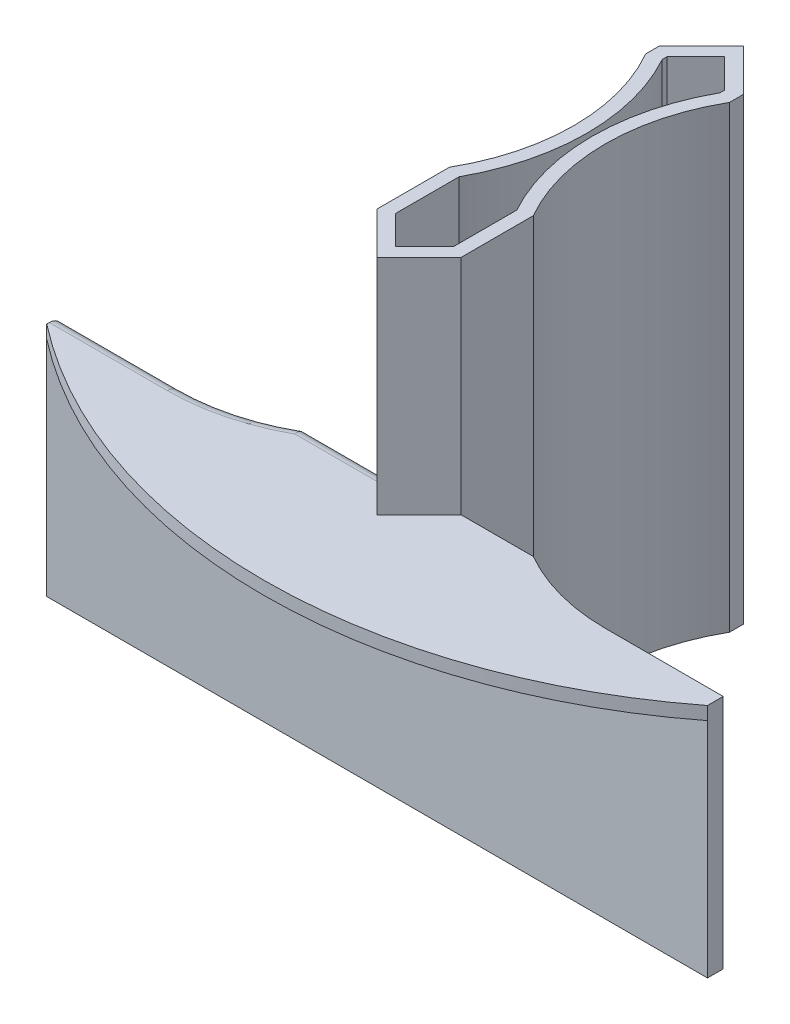
SolidWorks part; units mm, degrees
ref_plane "Front Plane" through (0, 0, 0) normal (0, 0, 1) x (1, 0, 0)
ref_plane "Top Plane" through (0, 0, 0) normal (0, 1, 0) x (1, 0, 0)
ref_plane "Right Plane" through (0, 0, 0) normal (1, 0, 0) x (0, 0, -1)
sketch "Sketch1" plane through (0, 0, 0) normal (0, 1, 0) x (1, 0, 0)
  line L0 (23.7595, 41.275) -> (41.275, 41.275) construction
  line L1 (-41.275, -41.275) -> (-23.7595, -41.275) construction
  line L2 (-41.275, -41.275) -> (-41.275, -23.7595) construction
  line L3 (-41.275, 41.275) -> (-23.7595, 41.275) construction
  line L4 (41.275, -41.275) -> (41.275, -23.7595) construction
  line L5 (-41.275, -41.275) -> (41.275, 41.275) construction
  line L6 (-41.275, 41.275) -> (41.275, -41.275) construction
  line L7 (41.275, 23.7595) -> (41.275, 41.275) construction
  line L8 (-41.275, 23.7595) -> (-41.275, 41.275) construction
  line L9 (23.7595, -41.275) -> (41.275, -41.275) construction
  line L10 (24.7569, 45.085) -> (45.085, 45.085) construction
  line L11 (45.085, 24.7569) -> (45.085, 45.085) construction
  line L12 (45.085, -45.085) -> (45.085, -24.7569) construction
  line L13 (24.7569, -45.085) -> (45.085, -45.085) construction
  line L14 (-45.085, -45.085) -> (-24.7569, -45.085) construction
  line L15 (-45.085, -45.085) -> (-45.085, -24.7569) construction
  line L16 (-45.085, 24.7569) -> (-45.085, 45.085) construction
  line L17 (-45.085, 45.085) -> (-24.7569, 45.085) construction
  line L19 (-51.435, -51.435) -> (51.435, -51.435) construction
  line L20 (-51.435, -51.435) -> (-51.435, 51.435) construction
  line L21 (-51.435, 51.435) -> (51.435, 51.435) construction
  line L22 (51.435, -51.435) -> (51.435, 51.435) construction
  line L23 (-51.435, -51.435) -> (51.435, 51.435) construction
  line L24 (-51.435, 51.435) -> (51.435, -51.435) construction
  arc A1 (-41.275, 23.7595) -> (-41.275, -23.7595) centre (0, 0) ccw construction
  arc A2 (23.7595, 41.275) -> (-23.7595, 41.275) centre (0, 0) ccw construction
  arc A3 (-23.7595, -41.275) -> (23.7595, -41.275) centre (0, 0) ccw construction
  arc A4 (41.275, -23.7595) -> (41.275, 23.7595) centre (0, 0) ccw construction
  arc A5 (45.085, -24.7569) -> (45.085, 24.7569) centre (0, 0) ccw construction
  arc A6 (-24.7569, -45.085) -> (24.7569, -45.085) centre (0, 0) ccw construction
  arc A7 (-45.085, 24.7569) -> (-45.085, -24.7569) centre (0, 0) ccw construction
  arc A8 (24.7569, 45.085) -> (-24.7569, 45.085) centre (0, 0) ccw construction
  point P0 (0, 0)
  dimension "D1" = 82.55
  dimension "D2" = 82.55
  dimension "D3" = 95.25
  dimension "D4" = 3.81
sketch "Sketch2" plane through (0, 0, 0) normal (0, 0, 1) x (1, 0, 0)
  line L0 (0, 48) -> (0, 0) construction
  line L1 (0, 0) -> (0, -9.15) construction
  line L2 (0, 48) -> (0, 101.975) construction
  dimension "Cage height" = 48
  dimension "Plate height" = 53.975
  dimension "D1" = 57.15
  dimension "D2" = 9.15
sketch "Sketch13" plane through (0, 0, 0) normal (0, 1, 0) x (1, 0, 0)
  line L0 (-51.435, -51.435) -> (51.435, -51.435) construction
  line L1 (-41.275, -41.275) -> (-23.7595, -41.275) construction
  line L2 (-41.275, -41.275) -> (-41.275, -23.7595) construction
  line L4 (-51.435, -51.435) -> (0, -51.435)
  line L5 (-41.275, -41.275) -> (-23.7595, -41.275)
  line L6 (-41.275, -41.275) -> (-41.275, -23.7595)
  line L9 (0, -47.625) -> (0, -51.435)
  line L10 (-51.435, 51.435) -> (51.435, -51.435) construction
  line L11 (-41.275, 23.7595) -> (-41.275, 41.275) construction
  line L12 (-51.435, -51.435) -> (-51.435, 51.435) construction
  line L13 (-51.435, 51.435) -> (-41.275, 41.275)
  line L14 (-41.275, 23.7595) -> (-41.275, 41.275)
  line L15 (-51.435, -51.435) -> (-51.435, 51.435)
  arc A0 (-23.7595, -41.275) -> (23.7595, -41.275) centre (0, 0) ccw construction
  arc A2 (-23.7595, -41.275) -> (0, -47.625) centre (0, 0) ccw
  arc A4 (-41.275, 23.7595) -> (-41.275, -23.7595) centre (0, 0) ccw construction
  arc A5 (-41.275, 23.7595) -> (-41.275, -23.7595) centre (0, 0) ccw
extrude "Boss-Extrude2" add sketch "Sketch13" along normal up to vertex (101.975 mm away) and the other way up to vertex (9.15 mm away) up to point (0, 101.975, 0) other way up to point (0, -9.15, 0)
sketch "Sketch15" plane through (0, 101.975, 0) normal (0, 1, 0) x (1, 0, 0)
  line L0 (0, 0) -> (-51.435, -51.435)
  line L1 (-51.435, -51.435) -> (0, -51.435)
  line L2 (0, -51.435) -> (0, 0)
  line L3 (-51.435, -51.435) -> (51.435, -51.435) construction
extrude "Cut-Extrude2" cut sketch "Sketch15" against normal up to vertex (53.975 mm away) up to point (0, 48, 0)
mirror "Mirror1" about plane through (-51.435, 101.975, 51.435) normal (1, 0, 0) of "Boss-Extrude2", "Cut-Extrude2"
sketch "Sketch16" plane through (0, -9.15, 0) normal (0, -1, 0) x (1, 0, 0)
  line L1 (-51.435, -51.435) -> (51.435, -51.435) construction
  circle A5 centre (-51.435, -13.335) radius 1.35
  dimension "D1" = 2.7
  dimension "D2" = 38.1
extrude "Cut-Extrude3" cut sketch "Sketch16" against normal through all
sketch "Sketch17" plane through (0, 101.975, 0) normal (0, 1, 0) x (1, 0, 0)
  line L0 (7.0944, 7.0944) -> (-7.0944, -7.0944)
  line L1 (7.0944, 7.0944) -> (-44.3406, 58.5294)
  line L2 (-7.0944, -7.0944) -> (-51.435, 37.2462)
  line L3 (-44.3406, 58.5294) -> (-51.435, 51.435)
  line L4 (-41.275, -41.275) -> (41.275, 41.275) construction
  line L5 (-61.595, 41.275) -> (-51.435, 51.435) construction
  line L6 (-51.435, -51.435) -> (-51.435, 51.435) construction
  line L7 (-51.435, 7.7321) -> (-51.435, 82.5591) construction
  line L8 (-95.7756, -7.0944) -> (-51.435, 37.2462)
  line L9 (-58.5294, 58.5294) -> (-51.435, 51.435)
  line L10 (-109.9644, 7.0944) -> (-58.5294, 58.5294)
  line L11 (-109.9644, 7.0944) -> (-95.7756, -7.0944)
  dimension "D1" = 20.066
extrude "Cut-Extrude4" cut sketch "Sketch17" against normal through all
sketch "Sketch22" plane through (0, 0, 0) normal (0, 1, 0) x (1, 0, 0)
  line L0 (-51.435, -51.435) -> (-51.435, 51.435) construction
  line L1 (-51.435, 51.435) -> (51.435, 51.435) construction
  circle A0 centre (-51.435, -12.065) radius 1.85
  dimension "D1" = 3.7
  dimension "D2" = 63.5
extrude "Cut-Extrude7" cut sketch "Sketch22" against normal through all both and the other way through all
sketch "Sketch23" plane through (0, 48, 0) normal (0, 1, 0) x (1, 0, 0)
  line L1 (0, -51.435) -> (28.575, -51.435)
  line L2 (0, -51.435) -> (0, -47.625)
  line L3 (0, -47.625) -> (28.575, -47.625)
  line L4 (28.575, -51.435) -> (28.575, -47.625)
  line L6 (-102.87, -51.435) -> (-131.445, -51.435)
  line L7 (-102.87, -51.435) -> (-102.87, -47.625)
  line L8 (-102.87, -47.625) -> (-131.445, -47.625)
  line L9 (-131.445, -51.435) -> (-131.445, -47.625)
  dimension "D1" = 28.575
extrude "Boss-Extrude3" add sketch "Sketch23" against normal up to surface (57.15 mm away) up to face at (-51.435, -9.15, 13.915)
sketch "Sketch24" plane through (0, 48, 0) normal (0, 1, 0) x (1, 0, 0)
  line L0 (28.575, -51.435) -> (-131.445, -51.435)
  arc A0 (-131.445, -51.435) -> (28.575, -51.435) centre (-51.435, 51.435) ccw
extrude "Boss-Extrude4" add sketch "Sketch24" against normal blind 3.175
fillet "Fillet1" radius 3.175 3 edges at (-117.1575, 48, 47.625) (-90.5733, 48, 46.0101) (-70.3527, 48, 41.275)
sketch "Sketch25" plane through (0, 101.975, 0) normal (0, 1, 0) x (1, 0, 0)
  line L24 (-44.45, 25.7711) -> (-51.435, 32.7561)
  line L25 (-51.435, 32.7561) -> (-58.42, 25.7711)
  line L26 (-58.42, 25.7711) -> (-58.42, 24.5934)
  line L27 (-58.42, -24.5934) -> (-58.42, -39.9599)
  line L28 (-58.42, -39.9599) -> (-51.435, -46.9449)
  line L29 (-51.435, -46.9449) -> (-44.45, -39.9599)
  line L30 (-44.45, -39.9599) -> (-44.45, -24.5934)
  line L31 (-44.45, 24.5934) -> (-44.45, 25.7711)
  line L35 (-58.42, -24.5934) -> (-58.42, -39.9599)
  line L36 (-58.42, -39.9599) -> (-51.435, -46.9449)
  line L37 (-51.435, -46.9449) -> (-44.45, -39.9599)
  line L38 (-44.45, -39.9599) -> (-44.45, -24.5934)
  line L49 (-44.45, 25.7711) -> (-44.45, 23.7595)
  line L50 (-58.42, 23.7595) -> (-58.42, 25.7711)
  line L51 (-51.435, 32.7561) -> (-44.45, 25.7711)
  line L52 (-58.42, 25.7711) -> (-51.435, 32.7561)
  line L53 (-44.45, 25.7711) -> (-44.45, 24.5934)
  line L54 (-58.42, 24.5934) -> (-58.42, 25.7711)
  line L55 (-51.435, 32.7561) -> (-44.45, 25.7711)
  line L56 (-58.42, 25.7711) -> (-51.435, 32.7561)
  arc A6 (-58.42, -24.5934) -> (-58.42, 24.5934) centre (-102.87, 0) ccw
  arc A7 (-44.45, 24.5934) -> (-44.45, -24.5934) centre (0, 0) ccw
  arc A8 (-58.42, -24.5934) -> (-54.6353, -15.9391) centre (-102.87, 0) ccw
  arc A9 (-44.45, 24.5934) -> (-48.087, 16.3791) centre (0, 0) ccw
  circle A16 centre (-51.435, 13.335) radius 4.525
  arc A17 (-48.087, 16.3791) -> (-54.783, 16.3791) centre (-51.435, 13.335) ccw
  circle A19 centre (-51.435, -12.065) radius 5.025
  arc A20 (-54.6353, -15.9391) -> (-48.2347, -15.9391) centre (-51.435, -12.065) ccw
  arc A21 (-54.783, 16.3791) -> (-58.42, 24.5934) centre (-102.87, 0) ccw
  arc A24 (-48.2347, -15.9391) -> (-44.45, -24.5934) centre (0, 0) ccw
  dimension "D1" = 3.175
  dimension "D2" = 3.175
  dimension "D3" = 3.175
  dimension "D4" = 3.175
extrude "Cut-Extrude8" cut sketch "Sketch25" against normal through all
sketch "Sketch26" plane through (0, -9.15, 0) normal (0, -1, 0) x (1, 0, 0)
  line L17 (-44.45, 44.45) -> (-48.26, 48.26)
  line L19 (-58.42, 44.45) -> (-54.61, 48.26)
  line L20 (-54.61, 48.26) -> (-87.0077, 48.26)
  line L26 (-58.42, -25.7711) -> (-51.435, -32.7561)
  line L27 (-51.435, -32.7561) -> (-44.45, -25.7711)
  line L28 (-44.45, -25.7711) -> (-44.45, -24.5934)
  line L29 (-44.45, 24.5934) -> (-44.45, 44.45)
  line L30 (-44.45, 44.45) -> (-24.5934, 44.45)
  line L31 (-15.8623, 48.26) -> (-87.0077, 48.26)
  line L32 (-78.2766, 44.45) -> (-58.42, 44.45)
  line L33 (-58.42, 44.45) -> (-58.42, 24.5934)
  line L34 (-58.42, -24.5934) -> (-58.42, -25.7711)
  line L39 (-44.45, 44.45) -> (-24.5934, 44.45)
  line L40 (-15.8623, 48.26) -> (-48.26, 48.26)
  line L41 (-78.2766, 44.45) -> (-58.42, 44.45)
  arc A8 (-44.45, 24.5934) -> (-44.45, -24.5934) centre (0, 0) ccw
  arc A9 (-15.8623, 48.26) -> (-24.5934, 44.45) centre (0, 0) ccw
  arc A10 (-78.2766, 44.45) -> (-87.0077, 48.26) centre (-102.87, 0) ccw
  arc A11 (-58.42, -24.5934) -> (-58.42, 24.5934) centre (-102.87, 0) ccw
  arc A13 (-15.8623, 48.26) -> (-24.5934, 44.45) centre (0, 0) ccw
  arc A14 (-78.2766, 44.45) -> (-87.0077, 48.26) centre (-102.87, 0) ccw
  dimension "D1" = 3.175
extrude "Cut-Extrude9" cut sketch "Sketch26" against normal offset from surface (53.975 mm away) 3.175 up to face at (-51.0718, 48, 50.289)
sketch "Sketch30" plane through (0, 101.975, 0) normal (0, 1, 0) x (1, 0, 0)
  line L16 (-44.45, 25.7711) -> (-51.435, 32.7561)
  line L17 (-51.435, 32.7561) -> (-58.42, 25.7711)
  line L18 (-58.42, 25.7711) -> (-58.42, 24.5934)
  line L19 (-58.42, -24.5934) -> (-58.42, -39.9599)
  line L20 (-58.42, -39.9599) -> (-51.435, -46.9449)
  line L21 (-51.435, -46.9449) -> (-44.45, -39.9599)
  line L22 (-44.45, -39.9599) -> (-44.45, -24.5934)
  line L23 (-44.45, 24.5934) -> (-44.45, 25.7711)
  line L24 (-44.45, 25.7711) -> (-51.435, 32.7561)
  line L25 (-51.435, 32.7561) -> (-58.42, 25.7711)
  line L26 (-58.42, 25.7711) -> (-58.42, 24.5934)
  line L27 (-58.42, -24.5934) -> (-58.42, -39.9599)
  line L28 (-58.42, -39.9599) -> (-51.435, -46.9449)
  line L29 (-51.435, -46.9449) -> (-44.45, -39.9599)
  line L30 (-44.45, -39.9599) -> (-44.45, -24.5934)
  line L31 (-44.45, 24.5934) -> (-44.45, 25.7711)
  arc A4 (-58.42, -24.5934) -> (-58.42, 24.5934) centre (-102.87, 0) ccw
  arc A5 (-44.45, 24.5934) -> (-44.45, -24.5934) centre (0, 0) ccw
  arc A6 (-58.42, -24.5934) -> (-58.42, 24.5934) centre (-102.87, 0) ccw
  arc A7 (-44.45, 24.5934) -> (-44.45, -24.5934) centre (0, 0) ccw
  dimension "D1" = 3.175
extrude "Cut-Extrude12" cut sketch "Sketch30" against normal offset from surface (82.55 mm away) 28.575 up to face at (-51.435, -9.15, 13.915)
equation "\"tightTol\"= 0.005in"
equation "\"normTol\"= 0.01in"
equation "\"looseTol\"= 0.02in"
equation "\"Cage height@Sketch2\"=48mm"
equation "\"Plate height@Sketch2\"=1.375+0.75"
equation "\"D1@Sketch17\"=0.75in+2*\"looseTol\""
equation "\"D1@Sketch22\"=3.7mm"
equation "\"D1@Sketch16\"=2.7mm"
